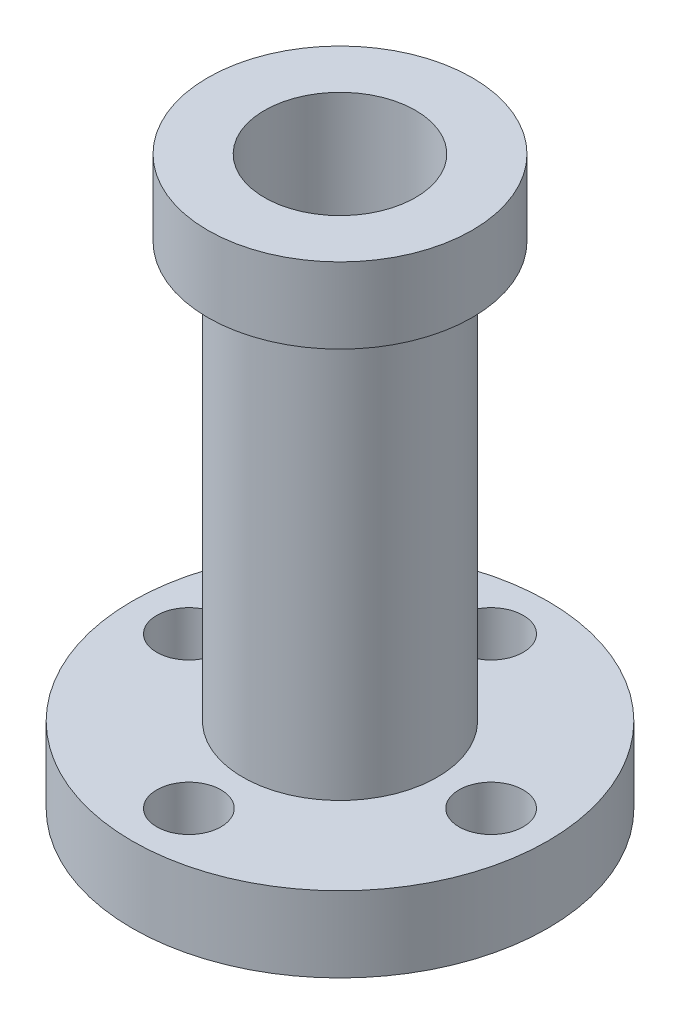
SolidWorks part; units mm, degrees
ref_plane "Front" through (0, 0, 0) normal (0, 0, 1) x (1, 0, 0)
ref_plane "Top" through (0, 0, 0) normal (0, 1, 0) x (1, 0, 0)
ref_plane "Right" through (0, 0, 0) normal (1, 0, 0) x (0, 0, -1)
sketch "Sketch2" plane through (0, 0, 0) normal (0, 0, 1) x (1, 0, 0)
  line L0 (0, 0) -> (0, 30) construction
  line L1 (4, 30) -> (4, 0)
  line L2 (4, 0) -> (11, 0)
  line L3 (11, 0) -> (11, 4)
  line L4 (11, 4) -> (5.15, 4)
  line L6 (7, 30) -> (4, 30)
  line L7 (0, 30) -> (4, 30) construction
  line L8 (5.15, 4) -> (5.15, 26)
  line L9 (5.15, 26) -> (7, 26)
  line L10 (7, 26) -> (7, 30)
  point P5 (5.7674, 30)
  point P13 (8.2751, 30)
  dimension "D1" = 30
  dimension "D2" = 4
  dimension "D3" = 22
  dimension "D4" = 4
  dimension "D5" = 8
  dimension "D6" = 10.3
  dimension "D7" = 14
revolve "Revolve1" add sketch "Sketch2" angle 360 about L0
hole_wizard "M3 Clearance Hole1" positions "Sketch3" profile "Sketch4" hole size "M3" standard "ANSI Metric"
sketch "Sketch3" plane through (0, 0, 0) normal (0, -1, 0) x (-1, 0, 0)
  line L0 (0, -8) -> (0, 0) construction
  line L1 (0, 0) -> (-8, 0) construction
  line L4 (0, 8) -> (0, 0) construction
  line L7 (8, 0) -> (0, 0) construction
  point P0 (0, -8)
  point P2 (-8, 0)
  point P4 (0, 8)
  point P6 (8, 0)
  dimension "D1" = 8
sketch "Sketch4" plane through (0, 0, 8) normal (1, 0, 0) x (0, 0, -1)
  line L0 (0, 0) -> (0, 5.0205)
  line L1 (0, 5.0205) -> (1.7, 3.999)
  line L2 (1.7, 3.999) -> (1.7, 0)
  line L5 (1.7, 0) -> (0, 0)
  line L10 (0, 5.0205) -> (-1.7, 3.999) construction
  line L11 (0, -6.35) -> (0, 107.95) construction
  dimension "Hole Dia." = 3.4
  dimension "Hole Depth" = 3.999
  dimension "Drill Angle" = 118
